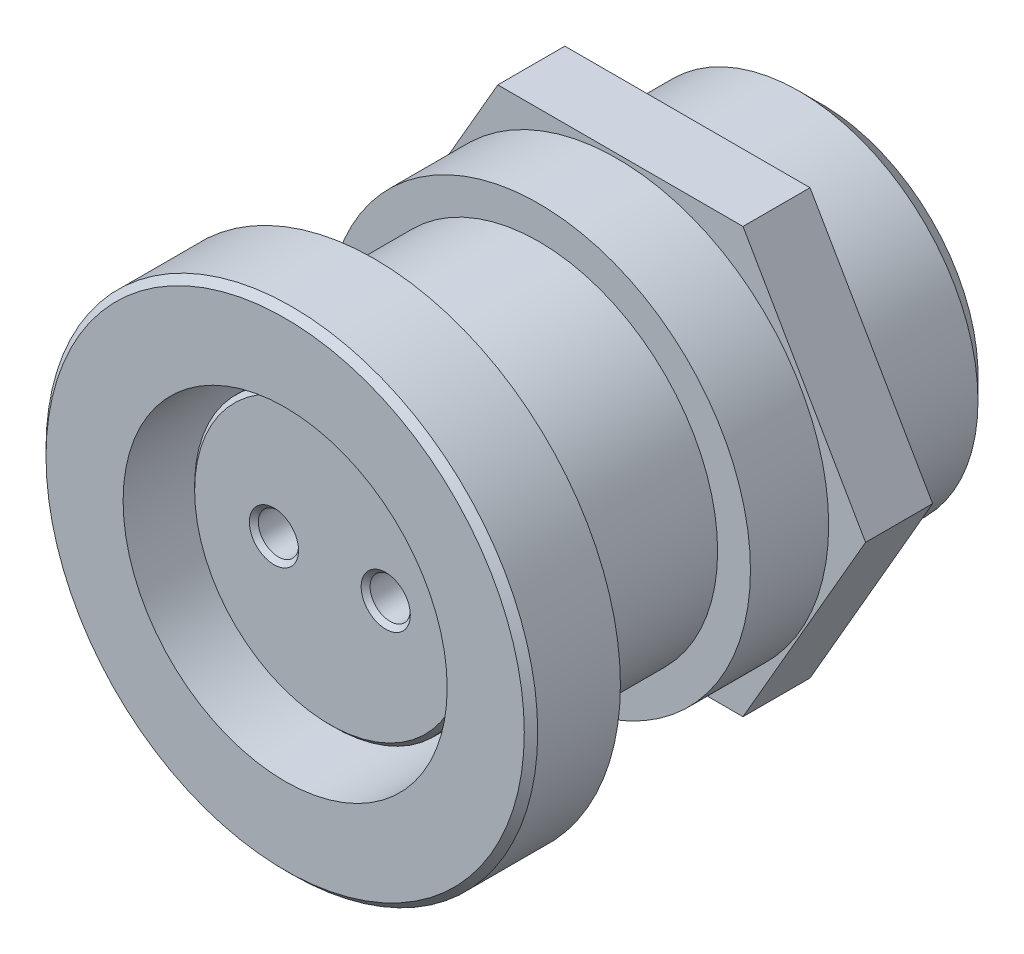
SolidWorks part; units mm, degrees
material "1060 Alloy"
ref_plane "Front Plane" through (0, 0, 0) normal (0, 0, 1) x (1, 0, 0)
ref_plane "Top Plane" through (0, 0, 0) normal (0, 1, 0) x (1, 0, 0)
ref_plane "Right Plane" through (0, 0, 0) normal (1, 0, 0) x (0, 0, -1)
sketch "Sketch1" plane through (0, 0, 0) normal (0, 0, 1) x (1, 0, 0)
  circle A0 centre (0, 0) radius 11
extrude "Extrude1" add sketch "Sketch1" along normal blind 4
sketch "Sketch3" plane through (0, 0, 0) normal (0, 0, -1) x (-1, 0, 0)
  circle A0 centre (0, 0) radius 8
extrude "Extrude3" add sketch "Sketch3" along normal blind 20
sketch "Sketch7" plane through (0, 0, 4) normal (0, 0, 1) x (1, 0, 0)
  circle A0 centre (0, 0) radius 7.25
extrude "Cut-Extrude5" cut sketch "Sketch7" against normal blind 16
sketch "Sketch4" plane through (0, 0, -12) normal (0, 0, 1) x (1, 0, 0)
  circle A0 centre (0, 0) radius 6.25
extrude "Extrude4" add sketch "Sketch4" along normal blind 14
chamfer "Chamfer1" distance 0.2 angle 45 1 edges at (6.25, 0, 2)
chamfer "Chamfer3" distance 0.3 angle 45 1 edges at (11, 0, 4)
sketch "Sketch5" plane through (0, 0, 0) normal (0, 0, -1) x (-1, 0, 0)
  circle A0 centre (0, 0) radius 10
  circle A1 centre (0, 0) radius 8.25
extrude "Cut-Extrude1" cut sketch "Sketch5" against normal blind 1.5
sketch "Sketch6" plane through (0, 0, 2) normal (0, 0, 1) x (1, 0, 0)
  line L0 (0, 0) -> (0, 6.05) construction
  line L1 (-6.05, 0) -> (6.05, 0) construction
  circle A5 centre (2.5, 0) radius 0.9
  circle A6 centre (-2.5, 0) radius 0.9
  circle A7 centre (0, 0) radius 6.05 construction
  dimension "D1" = 2.5
  dimension "D2" = 2.5
extrude "Cut-Extrude2" cut sketch "Sketch6" against normal blind 5
chamfer "Chamfer4" distance 0.2 angle 45 2 edges at (-1.6, 0, 2) (3.4, 0, 2)
sketch "Sketch8" plane through (0, 0, -20) normal (0, 0, -1) x (-1, 0, 0)
  circle A0 centre (0, 0) radius 6
extrude "Cut-Extrude6" cut sketch "Sketch8" against normal blind 2
chamfer "Chamfer5" distance 1 angle 45 1 edges at (-8, 0, -20)
sketch "Sketch10" plane through (0, 0, 0) normal (0, 0, -1) x (-1, 0, 0)
  circle A0 centre (0, 0) radius 9.4691
  circle A1 centre (0, 0) radius 8
  circle A2 centre (0, 0) radius 8 construction
extrude "Extrude6" add sketch "Sketch10" along normal blind 3.5 from offset 7.35
sketch "Sketch9" plane through (0, 0, -18) normal (0, 0, -1) x (-1, 0, 0)
  line L0 (-5.4848, 9.5) -> (5.4848, 9.5)
  line L1 (5.4848, 9.5) -> (10.9697, 0)
  line L2 (10.9697, 0) -> (5.4848, -9.5)
  line L3 (5.4848, -9.5) -> (-5.4848, -9.5)
  line L4 (-5.4848, -9.5) -> (-10.9697, 0)
  line L5 (-10.9697, 0) -> (-5.4848, 9.5)
  line L6 (0, 9.5) -> (0, -9.5) construction
  dimension "D1" = 19
  dimension "D2" = 19
extrude "Extrude5" add sketch "Sketch9" along normal blind 3 from offset 7 offset against normal yes
